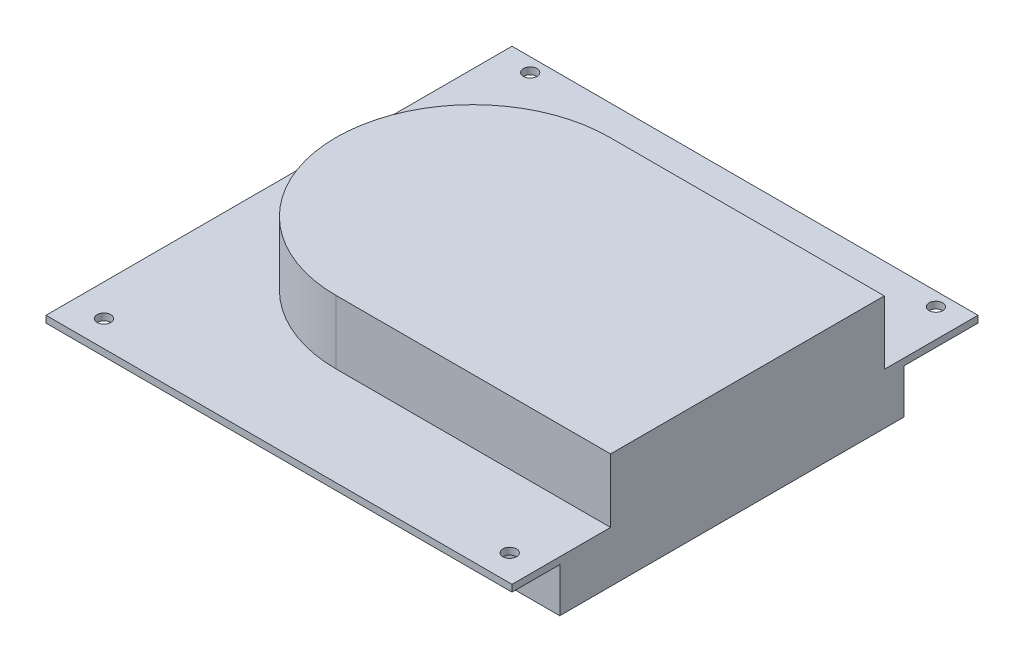
SolidWorks part; units mm, degrees
ref_plane "Front Plane" through (0, 0, 0) normal (0, 0, 1) x (1, 0, 0)
ref_plane "Top Plane" through (0, 0, 0) normal (0, 1, 0) x (1, 0, 0)
ref_plane "Right Plane" through (0, 0, 0) normal (1, 0, 0) x (0, 0, -1)
sketch "Sketch1" plane through (0, 0, 0) normal (0, 1, 0) x (1, 0, 0)
  line L1 (0, 0) -> (104.14, 0)
  line L2 (0, 0) -> (0, 104.14)
  line L3 (0, 104.14) -> (104.14, 104.14)
  line L4 (104.14, 0) -> (104.14, 104.14)
  circle A0 centre (7.112, 101.092) radius 1.524
  circle A1 centre (97.79, 101.092) radius 1.524
  circle A2 centre (7.112, 5.842) radius 1.524
  circle A3 centre (97.79, 5.842) radius 1.524
  dimension "D7" = 3.048
  dimension "D1" = 104.14
  dimension "D2" = 104.14
  dimension "D3" = 95.25
  dimension "D4" = 90.678
  dimension "D5" = 7.112
  dimension "D6" = 5.842
extrude "Boss-Extrude1" add sketch "Sketch1" along normal blind 1.524
sketch "Sketch2" plane through (0, 1.524, 0) normal (0, 1, 0) x (1, 0, 0)
  line L0 (104.14, 0) -> (104.14, 104.14) construction
  line L1 (104.14, 83.1978) -> (42.7986, 83.1978)
  line L2 (104.14, 83.1978) -> (104.14, 22.024)
  line L3 (104.14, 22.024) -> (42.7986, 22.024)
  line L4 (42.7986, 83.1978) -> (42.7986, 22.024)
  circle A0 centre (42.7986, 52.6109) radius 30.5869
  line M8 (104.14, 0) -> (104.14, 104.14)
extrude "Boss-Extrude2" add sketch "Sketch2" along normal blind 14.224 contours A0 L3 L1 M8 | L4 A0 | L4 A0
sketch "Sketch3" plane through (0, 0, 0) normal (0, -1, 0) x (1, 0, 0)
  line L0 (104.14, 0) -> (104.14, -104.14) construction
  line L1 (104.14, -87.5502) -> (86.0038, -87.5502)
  line L2 (104.14, -87.5502) -> (104.14, -10.677)
  line L3 (104.14, -10.677) -> (86.0038, -10.677)
  line L4 (86.0038, -87.5502) -> (86.0038, -10.677)
extrude "Boss-Extrude3" add sketch "Sketch3" along normal blind 9.906
sketch "Sketch4" plane through (0, -9.906, 0) normal (0, -1, 0) x (1, 0, 0)
  text T0 "USB x2"
  text T1 "Eth"
  text T2 "HDMI"
  text T3 "Power"
sketch "Sketch5" plane through (0, 0, 0) normal (0, -1, 0) x (1, 0, 0)
  line L0 (0, -104.14) -> (0, 0) construction
  line L1 (0, -73.9756) -> (17.1398, -73.9756)
  line L2 (0, -73.9756) -> (0, -22.38)
  line L3 (0, -22.38) -> (17.1398, -22.38)
  line L4 (17.1398, -73.9756) -> (17.1398, -22.38)
extrude "Boss-Extrude4" add sketch "Sketch5" along normal blind 9.906
sketch "Sketch6" plane through (0, -9.906, 0) normal (0, -1, 0) x (1, 0, 0)
  text T0 "USB"
  text T1 "USB"
